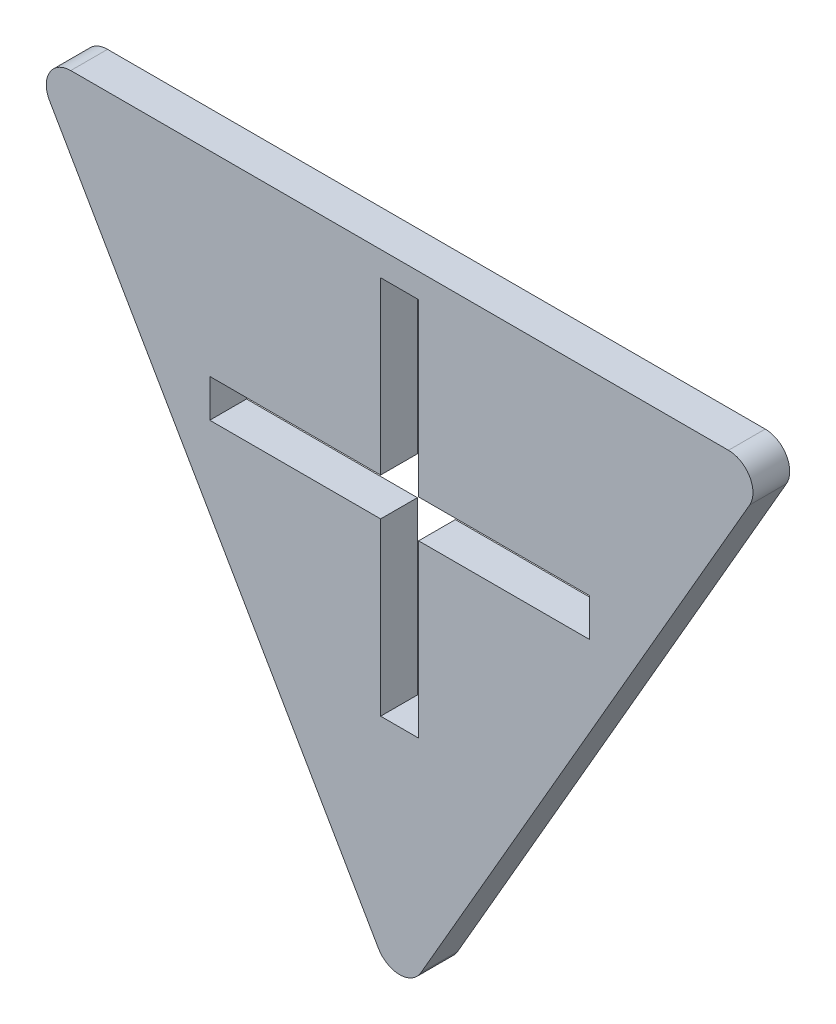
SolidWorks part; units mm, degrees
ref_plane "Front Plane" through (0, 0, 0) normal (0, 0, 1) x (1, 0, 0)
ref_plane "Top Plane" through (0, 0, 0) normal (0, 1, 0) x (1, 0, 0)
ref_plane "Right Plane" through (0, 0, 0) normal (1, 0, 0) x (0, 0, -1)
sketch "Sketch1" plane through (0, 0, 0) normal (0, 0, 1) x (1, 0, 0)
  line L1 (-1.55, 15.5) -> (1.55, 15.5)
  line L2 (-1.55, 15.5) -> (-1.55, -15.5)
  line L3 (-1.55, -15.5) -> (1.55, -15.5)
  line L4 (1.55, 15.5) -> (1.55, -15.5)
  line L5 (-1.55, 15.5) -> (1.55, -15.5) construction
  line L6 (-1.55, -15.5) -> (1.55, 15.5) construction
  line L7 (-15.5, 1.55) -> (15.5, 1.55)
  line L8 (-15.5, 1.55) -> (-15.5, -1.55)
  line L9 (-15.5, -1.55) -> (15.5, -1.55)
  line L10 (15.5, 1.55) -> (15.5, -1.55)
  line L11 (-15.5, 1.55) -> (15.5, -1.55) construction
  line L12 (-15.5, -1.55) -> (15.5, 1.55) construction
  line L13 (26.8468, 17.5) -> (-26.8468, 17.5)
  line L14 (-28.5788, 14.5) -> (-1.7321, -32)
  line L15 (1.7321, -32) -> (28.5788, 14.5)
  circle A0 centre (0, 0) radius 17.5 construction
  arc A1 (1.7321, -32) -> (-1.7321, -32) centre (0, -31) cw
  arc A2 (28.5788, 14.5) -> (26.8468, 17.5) centre (26.8468, 15.5) ccw
  arc A3 (-26.8468, 17.5) -> (-28.5788, 14.5) centre (-26.8468, 15.5) ccw
  point P0 (0, 0)
  point P6 (0, 0)
  dimension "D5" = 35
  dimension "D6" = 2
  dimension "D1" = 31
  dimension "D2" = 3.1
  dimension "D3" = 3.1
  dimension "D4" = 31
extrude "Boss-Extrude1" add sketch "Sketch1" along normal mid plane 3 contours L13 A3 L14 A1 L15 A2 L7 L10 L9 L4 L3 L2 L8 L1
